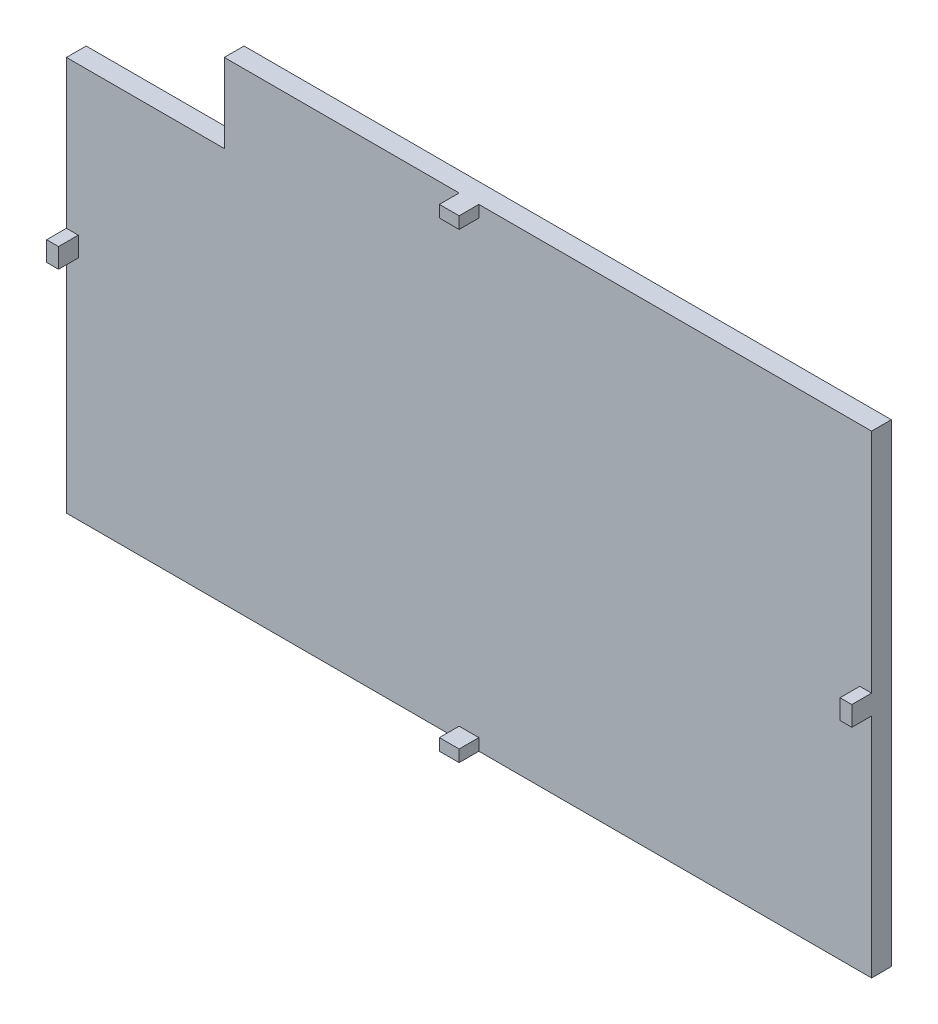
SolidWorks part; units mm, degrees
ref_plane "Plano frontal" through (0, 0, 0) normal (0, 0, 1) x (1, 0, 0)
ref_plane "Plano superior" through (0, 0, 0) normal (0, 1, 0) x (1, 0, 0)
ref_plane "Plano direito" through (0, 0, 0) normal (1, 0, 0) x (0, 0, -1)
sketch "Esboço1" plane through (0, 0, 0) normal (0, 0, 1) x (1, 0, 0)
  line L1 (-51.4207, 30.869) -> (152.5793, 30.869)
  line L2 (-51.4207, 30.869) -> (-51.4207, -89.131)
  line L3 (-51.4207, -89.131) -> (152.5793, -89.131)
  line L4 (152.5793, 30.869) -> (152.5793, -89.131)
  dimension "D1" = 204
  dimension "D2" = 120
extrude "Ressalto-extrusão1" add sketch "Esboço1" along normal blind 5 contours L1 L4 L3 L2
sketch "Esboço2" plane through (0, 0, 5) normal (0, 0, 1) x (1, 0, 0)
  line L1 (-51.4207, 30.869) -> (152.5793, 30.869) construction
  line L2 (53.0793, 30.869) -> (48.0793, 30.869)
  line L3 (53.0793, 30.869) -> (53.0793, 27.869)
  line L4 (53.0793, 27.869) -> (48.0793, 27.869)
  line L5 (48.0793, 30.869) -> (48.0793, 27.869)
  line L6 (-51.4207, -89.131) -> (152.5793, -89.131) construction
  line L7 (53.0793, -89.131) -> (48.0793, -89.131)
  line L8 (53.0793, -89.131) -> (53.0793, -86.131)
  line L10 (53.0793, -86.131) -> (48.0793, -86.131)
  line L11 (48.0793, -89.131) -> (48.0793, -86.131)
  line L12 (-51.4207, 30.869) -> (-51.4207, -89.131) construction
  line L13 (-51.4207, -26.631) -> (-48.4207, -26.631)
  line L15 (-51.4207, -26.631) -> (-51.4207, -31.631)
  line L16 (-51.4207, -31.631) -> (-48.4207, -31.631)
  line L17 (-48.4207, -26.631) -> (-48.4207, -31.631)
  line L18 (152.5793, 30.869) -> (152.5793, -89.131) construction
  line L19 (152.5793, -26.631) -> (149.5793, -26.631)
  line L20 (152.5793, -26.631) -> (152.5793, -31.631)
  line L21 (152.5793, -31.631) -> (149.5793, -31.631)
  line L22 (149.5793, -26.631) -> (149.5793, -31.631)
  dimension "D2" = 3
  dimension "D3" = 3
  dimension "D1" = 3
  dimension "D4" = 3
  dimension "D5" = 5
  dimension "D6" = 5
  dimension "D7" = 5
  dimension "D8" = 5
  dimension "D9" = 57.5
  dimension "D10" = 57.5
  dimension "D11" = 99.5
  dimension "D12" = 99.5
extrude "Ressalto-extrusão2" add sketch "Esboço2" along normal blind 5 contours L2 L5 L4 L3 | L15 L16 L17 L13 | L7 L11 L10 L8 | L20 L21 L22 L19
sketch "Esboço3" plane through (0, 0, 0) normal (0, 0, -1) x (-1, 0, 0)
  line L1 (51.4207, 30.869) -> (11.4207, 30.869)
  line L2 (51.4207, 30.869) -> (51.4207, 10.869)
  line L3 (51.4207, 10.869) -> (11.4207, 10.869)
  line L4 (11.4207, 30.869) -> (11.4207, 10.869)
  dimension "D1" = 40
  dimension "D2" = 20
extrude "Corte-extrusão1" cut sketch "Esboço3" against normal blind 10
